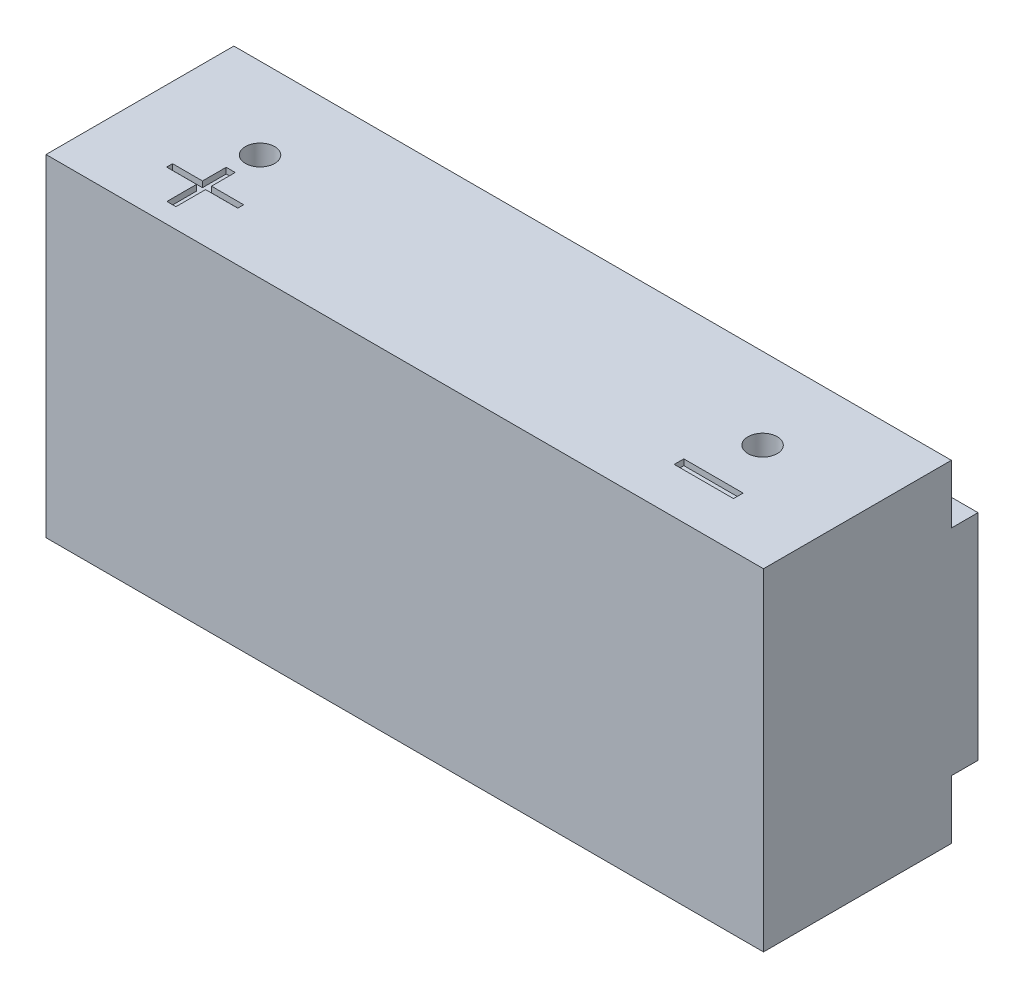
SolidWorks part; units mm, degrees
material "Subpack"
ref_plane "X-Y Datum" through (0, 0, 0) normal (0, 0, 1) x (1, 0, 0)
ref_plane "X-Z Datum" through (0, 0, 0) normal (0, 1, 0) x (1, 0, 0)
ref_plane "Y-Z Datum" through (0, 0, 0) normal (1, 0, 0) x (0, 0, -1)
sketch "Sketch1" plane through (0, 0, 0) normal (0, 1, 0) x (1, 0, 0)
  line L1 (0, 0) -> (310.6395, 0)
  line L2 (0, 0) -> (0, 92.8692)
  line L3 (0, 92.8692) -> (310.6395, 92.8692)
  line L4 (310.6395, 0) -> (310.6395, 92.8692)
  dimension "D1" = 92.8692
  dimension "D2" = 310.6395
extrude "Boss-Extrude1" add sketch "Sketch1" along normal blind 143.6878
sketch "Sketch2" plane through (0, 143.6878, 0) normal (0, 1, 0) x (1, 0, 0)
  line L0 (0, 46.1416) -> (0, 0) construction
  line L1 (0, 92.8692) -> (0, 0) construction
  line L2 (0, 46.1416) -> (46.5328, 46.1416) construction
  line L3 (155.3197, 92.8692) -> (155.3197, -12.4635) construction
  line L4 (310.6395, 92.8692) -> (0, 92.8692) construction
  circle A0 centre (46.5328, 46.1416) radius 6.35
  circle A1 centre (264.1067, 46.1416) radius 6.35
  dimension "D1" = 46.1416
extrude "Cut-Extrude1" cut sketch "Sketch2" against normal through all
sketch "Sketch3" plane through (0, 143.6878, 0) normal (0, 1, 0) x (1, 0, 0)
  line L0 (46.5328, 46.1416) -> (46.5328, 92.8692) construction
  line L1 (310.6395, 92.8692) -> (0, 92.8692) construction
  line L2 (46.5328, 46.1416) -> (46.5328, 0) construction
  line L3 (0, 0) -> (310.6395, 0) construction
  line L9 (0, 46.4346) -> (347.5244, 46.4346) construction
  line L10 (0, 92.8692) -> (0, 0) construction
  line L11 (0, 81.3384) -> (310.8274, 81.3384)
  line L12 (310.8274, 94.0384) -> (310.8274, 81.3384)
  line L13 (0, 94.0384) -> (310.8274, 94.0384)
  line L14 (0, 94.0384) -> (0, 81.3384)
extrude "Cut-Extrude2" cut sketch "Sketch3" against normal blind 25.4
ref_plane "Plane1" through (0, 71.8439, 0) normal (0, 1, 0) x (1, 0, 0)
mirror "Mirror1" about plane through (0, 71.8439, 0) normal (0, 1, 0) of "Cut-Extrude2"
ref_plane "Plane2" through (0, 0, -46.4346) normal (0, 0, 1) x (1, 0, 0)
sketch "Sketch4" plane through (0, 143.6878, 0) normal (0, 1, 0) x (1, 0, 0)
  line L0 (43.7863, 21.3915) -> (43.7863, 8.5645)
  line L1 (43.7863, 34.2184) -> (47.6954, 34.2184)
  line L2 (43.7863, 34.2184) -> (43.7863, 23.9569)
  line L3 (43.7863, 8.5645) -> (47.6954, 8.5645)
  line L4 (47.6954, 34.2184) -> (47.6954, 23.9569)
  line L5 (30.8371, 23.9569) -> (43.7863, 23.9569)
  line L6 (30.8371, 23.9569) -> (30.8371, 21.3915)
  line L7 (30.8371, 21.3915) -> (43.7863, 21.3915)
  line L8 (61.6218, 23.9569) -> (61.6218, 21.3915)
  line L9 (252.1938, 23.9569) -> (277.8477, 23.9569)
  line L10 (252.1938, 23.9569) -> (252.1938, 19.8034)
  line L11 (252.1938, 19.8034) -> (277.8477, 19.8034)
  line L12 (277.8477, 23.9569) -> (277.8477, 19.8034)
  line L13 (47.6954, 21.3915) -> (47.6954, 8.5645)
  line L14 (47.6954, 21.3915) -> (61.6218, 21.3915)
  line L15 (47.6954, 23.9569) -> (61.6218, 23.9569)
extrude "Cut-Extrude3" cut sketch "Sketch4" against normal blind 2.54
ref_plane "Plane3" through (0, 71.8439, 0) normal (0, 1, 0) x (1, 0, 0)
